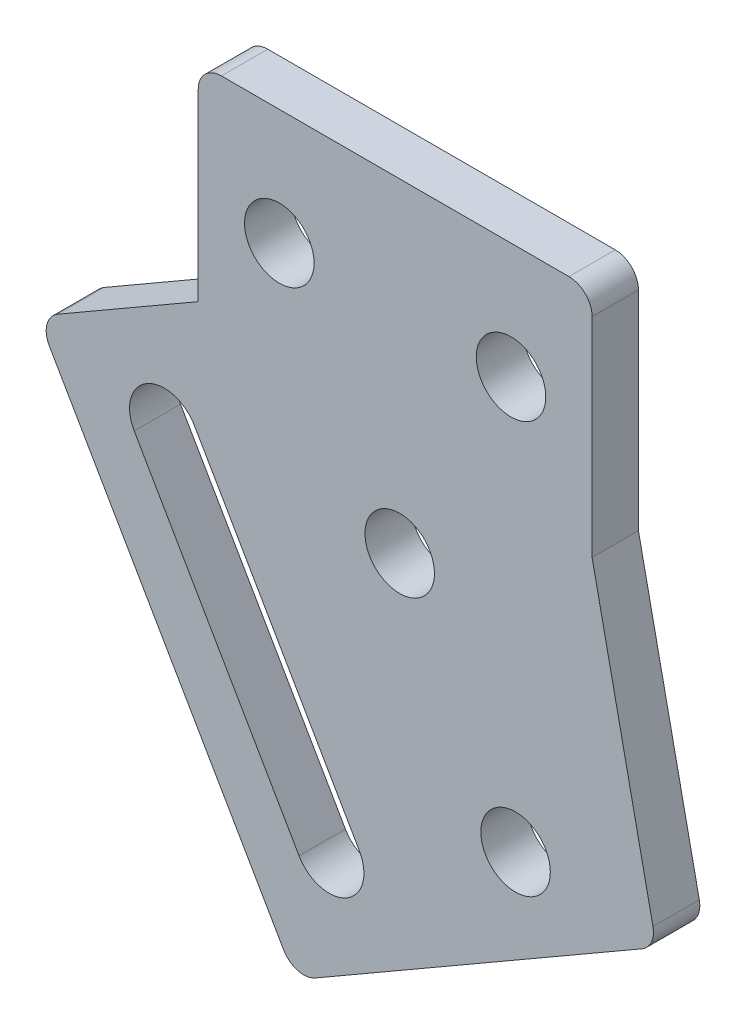
SolidWorks part; units mm, degrees
material "环氧板3240"
ref_plane "前视基准面" through (0, 0, 0) normal (0, 0, 1) x (1, 0, 0)
ref_plane "上视基准面" through (0, 0, 0) normal (0, 1, 0) x (1, 0, 0)
ref_plane "右视基准面" through (0, 0, 0) normal (1, 0, 0) x (0, 0, -1)
other "Configuration Table"
sketch "草图1" plane through (0, 0, 0) normal (0, 0, 1) x (1, 0, 0)
  line L0 (-17, 0) -> (0, 0)
  line L3 (-17, -8.9378) -> (-5.884, -28.1913)
  line L4 (-5.884, -28.1913) -> (2.7763, -23.1913)
  line L7 (-1.5538, -25.6913) -> (-16.3868, 0) construction
  line L9 (0, -10) -> (-17, -10) construction
  line L10 (0, -10) -> (0, 0)
  line L11 (-8.3038, -14) -> (-12.634, -16.5) construction
  line L12 (2.7763, -23.1913) -> (0, -10)
  line L13 (-17, 0) -> (-17, -8.9378)
  line L14 (-17, -5) -> (0, -5) construction
  circle A0 centre (-3.3038, -22.6603) radius 1.5
  circle A1 centre (-13.5, -5) radius 1.5
  circle A2 centre (-8.3038, -14) radius 1.5
  circle A3 centre (-3.5, -5) radius 1.5
  dimension "D6" = 3
  dimension "D8" = 10
  dimension "D2" = 10
  dimension "D9" = 10
  dimension "D10" = 2
  dimension "D5" = 4
  dimension "D3" = 2
  dimension "D7" = 2
  dimension "D1" = 10
  dimension "D4" = 5
  dimension "D11" = 60
extrude "凸台-拉伸1" add sketch "草图1" along normal blind 2
sketch "草图2" plane through (-16.6202, -9.5957, 0) normal (-0.866, -0.5, 0) x (0, 0, 1)
  line L0 (2, 0.7596) -> (0, 0.7596) construction
  line L1 (2, 0.7596) -> (0, 0.7596)
  line L2 (2, 0.7596) -> (2, -21.4724)
  line L3 (2, -21.4724) -> (0, -21.4724)
  line L4 (0, 0.7596) -> (0, -21.4724)
  line L5 (2, 0.7596) -> (0, -21.4724) construction
  line L6 (2, -21.4724) -> (0, 0.7596) construction
  line L7 (0, 0.7596) -> (0, -21.4724) construction
  point P5 (1, -10.3564)
extrude "凸台-拉伸2" add sketch "草图2" along normal blind 8
sketch "草图3" plane through (0, 0, 0) normal (0, 0, -1) x (-1, 0, 0)
  line L0 (20.4641, -10.9378) -> (9.3481, -30.1913) construction
  line L2 (23.9282, -12.9378) -> (17, -8.9378) construction
  line L3 (12.8122, -32.1913) -> (-2.7763, -23.1913) construction
  line L5 (11.3481, -26.7272) -> (18.4641, -14.4019) construction
  line L6 (10.049, -25.9772) -> (17.1651, -13.6519)
  line L7 (12.6471, -27.4772) -> (19.7631, -15.1519)
  arc A1 (10.049, -25.9772) -> (12.6471, -27.4772) centre (11.3481, -26.7272) ccw
  arc A2 (19.7631, -15.1519) -> (17.1651, -13.6519) centre (18.4641, -14.4019) ccw
  point P8 (14.9061, -20.5646)
  dimension "D1" = 3
  dimension "D2" = 4
  dimension "D3" = 4
extrude "切除-拉伸1" cut sketch "草图3" against normal blind 5
fillet "圆角1" radius 1 5 edges at (2.7763, -23.1913, 1) (-12.8122, -32.1913, 1) (-23.9282, -12.9378, 1) (-17, 0, 1) (0, 0, 1)
